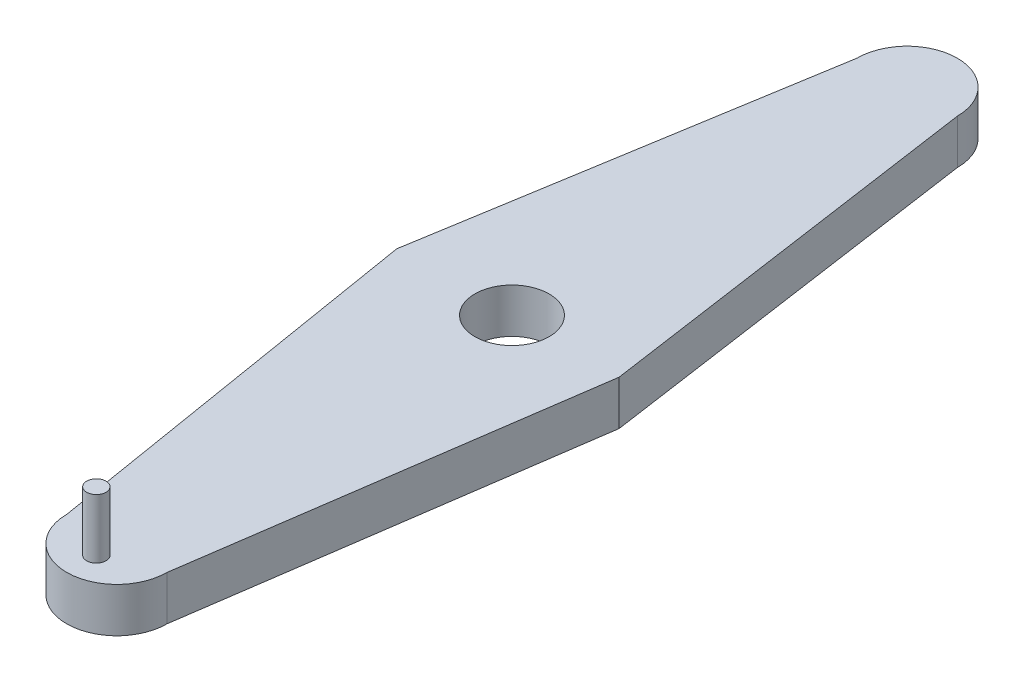
SolidWorks part; units mm, degrees
material "AISI 1020 Steel, Cold Rolled"
ref_plane "Front Plane" through (0, 0, 0) normal (0, 0, 1) x (1, 0, 0)
ref_plane "Top Plane" through (0, 0, 0) normal (0, 1, 0) x (1, 0, 0)
ref_plane "Right Plane" through (0, 0, 0) normal (1, 0, 0) x (0, 0, -1)
sketch "Sketch1" plane through (0, 0, 0) normal (0, 1, 0) x (1, 0, 0)
  line L0 (-77.618, 0) -> (-33.8206, 266.1794)
  line L1 (0, -300) -> (0, -318.9637) construction
  line L2 (33.8206, 266.1794) -> (72.1766, 0)
  line L3 (-160.5166, 0) -> (105.4185, 0) construction
  line L4 (0, -266.1794) -> (0, 266.1794) construction
  line L5 (0, 300) -> (0, 318.9637) construction
  line L6 (33.8206, -266.1794) -> (72.1766, 0)
  line L7 (-77.618, 0) -> (-33.8206, -266.1794)
  arc A0 (33.8206, 266.1794) -> (-33.8206, 266.1794) centre (0, 266.1794) ccw
  arc A1 (33.8206, -266.1794) -> (-33.8206, -266.1794) centre (0, -266.1794) cw
  point P14 (0, 0)
  dimension "D1" = 600
extrude "Boss-Extrude1" add sketch "Sketch1" along normal blind 30
sketch "Sketch2" plane through (0, 30, 0) normal (0, 1, 0) x (1, 0, 0)
  circle A0 centre (0, 0) radius 25
  dimension "D1" = 50
extrude "Cut-Extrude1" cut sketch "Sketch2" against normal blind 30
sketch "Sketch3" plane through (0, 30, 0) normal (0, 1, 0) x (1, 0, 0)
  circle A0 centre (0, -280) radius 6.505
  arc A1 (-33.8206, -266.1794) -> (33.8206, -266.1794) centre (0, -266.1794) ccw construction
  point P5 (0, -300)
  dimension "D2" = 13.01
  dimension "D1" = 20
extrude "Boss-Extrude2" add sketch "Sketch3" along normal blind 40
